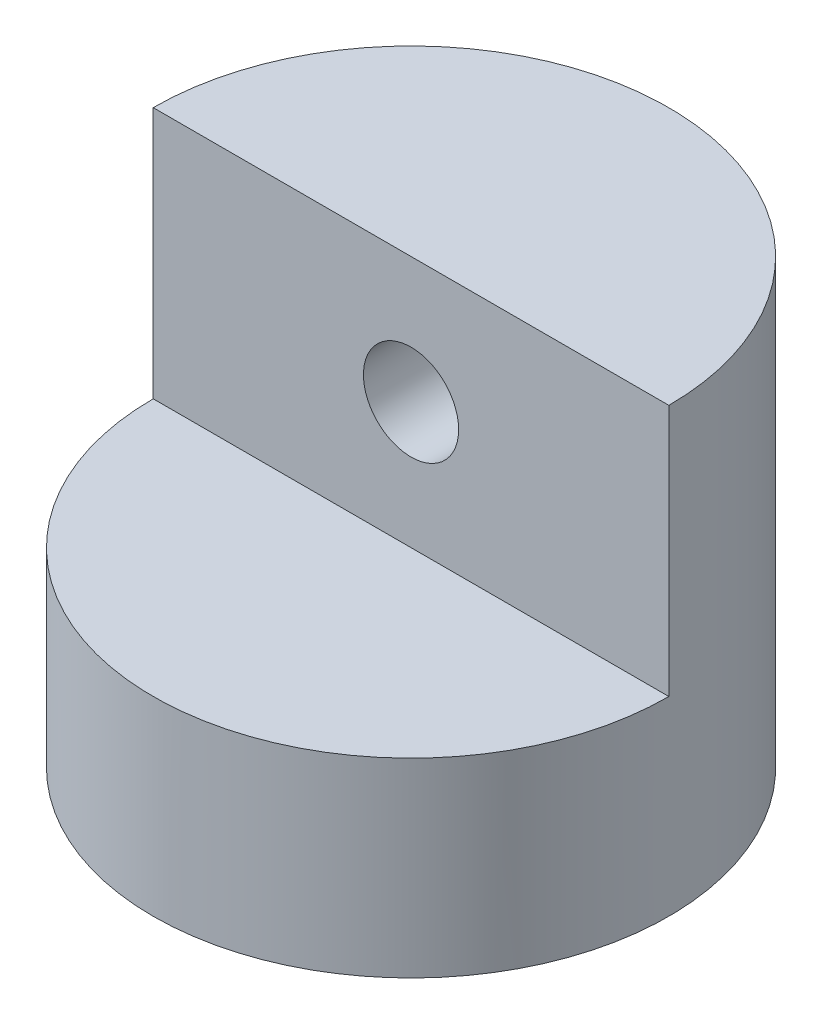
SolidWorks part; units mm, degrees
ref_plane "Front Plane" through (0, 0, 0) normal (0, 0, 1) x (1, 0, 0)
ref_plane "Top Plane" through (0, 0, 0) normal (0, 1, 0) x (1, 0, 0)
ref_plane "Right Plane" through (0, 0, 0) normal (1, 0, 0) x (0, 0, -1)
sketch "Sketch1" plane through (0, 0, 0) normal (0, 1, 0) x (1, 0, 0)
  line L0 (-32.5, 0) -> (32.5, 0) construction
  circle A0 centre (0, 0) radius 32.5
  dimension "D1" = 65
extrude "Boss-Extrude1" add sketch "Sketch1" along normal blind 55.788
sketch "Sketch2" plane through (0, 55.788, 0) normal (0, 1, 0) x (1, 0, 0)
  line L0 (-32.5, 0) -> (32.5, 0) construction
  circle A0 centre (0, 0) radius 32.5 construction
  circle M1 centre (0, 0) radius 32.5
extrude "Cut-Extrude1" cut sketch "Sketch2" against normal blind 31.788 contours L0 M1
sketch "Sketch3" plane through (0, 0, 0) normal (0, -1, 0) x (-1, 0, 0)
  circle A0 centre (0, 0) radius 6
  circle A1 centre (0, 0) radius 8
  dimension "D1" = 12
  dimension "D2" = 16
extrude "Boss-Extrude2" add sketch "Sketch3" along normal blind 2
sketch "Sketch5" plane through (0, 0, 0) normal (0, 0, 1) x (1, 0, 0)
  line L0 (0, 55.788) -> (0, 24) construction
  line L1 (-32.5, 55.788) -> (32.5, 55.788) construction
  line L2 (-32.5, 24) -> (32.5, 24) construction
  circle A0 centre (0, 39.894) radius 6
  dimension "D1" = 12
extrude "Cut-Extrude3" cut sketch "Sketch5" against normal blind 46
